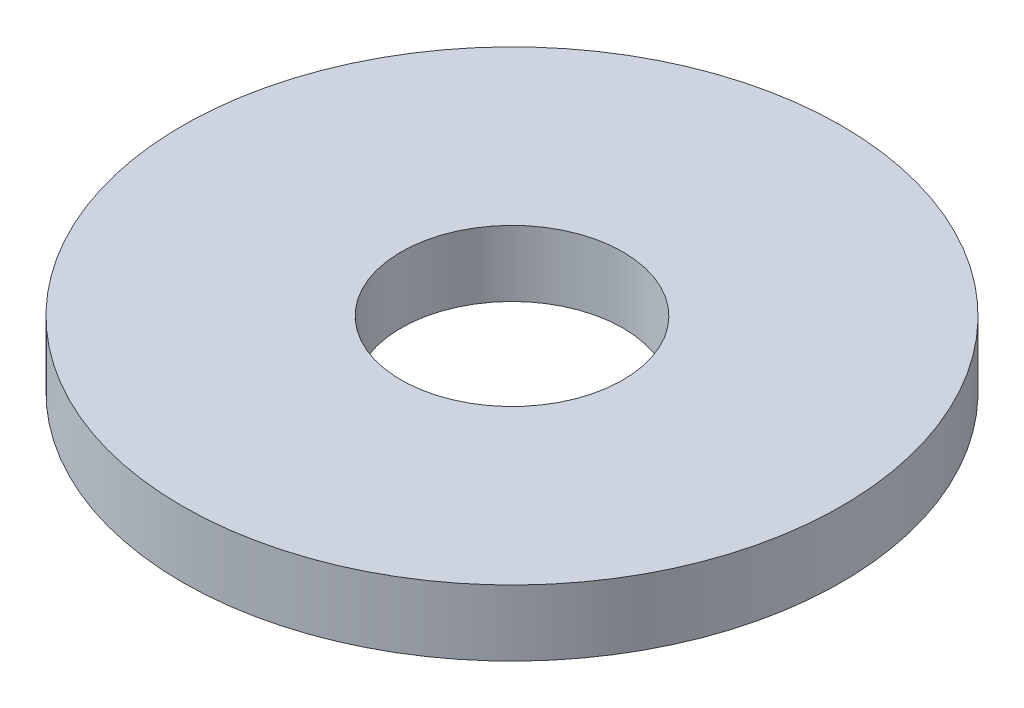
SolidWorks part; units mm, degrees
material "Plain Carbon Steel"
ref_plane "Front Plane" through (0, 0, 0) normal (0, 0, 1) x (1, 0, 0)
ref_plane "Top Plane" through (0, 0, 0) normal (0, 1, 0) x (1, 0, 0)
ref_plane "Right Plane" through (0, 0, 0) normal (1, 0, 0) x (0, 0, -1)
sketch "Sketch1" plane through (0, 0, 0) normal (0, 1, 0) x (1, 0, 0)
  circle A0 centre (0, 0) radius 1.5
extrude "Boss-Extrude1" add sketch "Sketch1" along normal blind 0.3
sketch "Sketch2" plane through (0, 0, 0) normal (0, -1, 0) x (1, 0, 0)
  circle A0 centre (0, 0) radius 0.505
extrude "Cut-Extrude1" cut sketch "Sketch2" against normal through all
